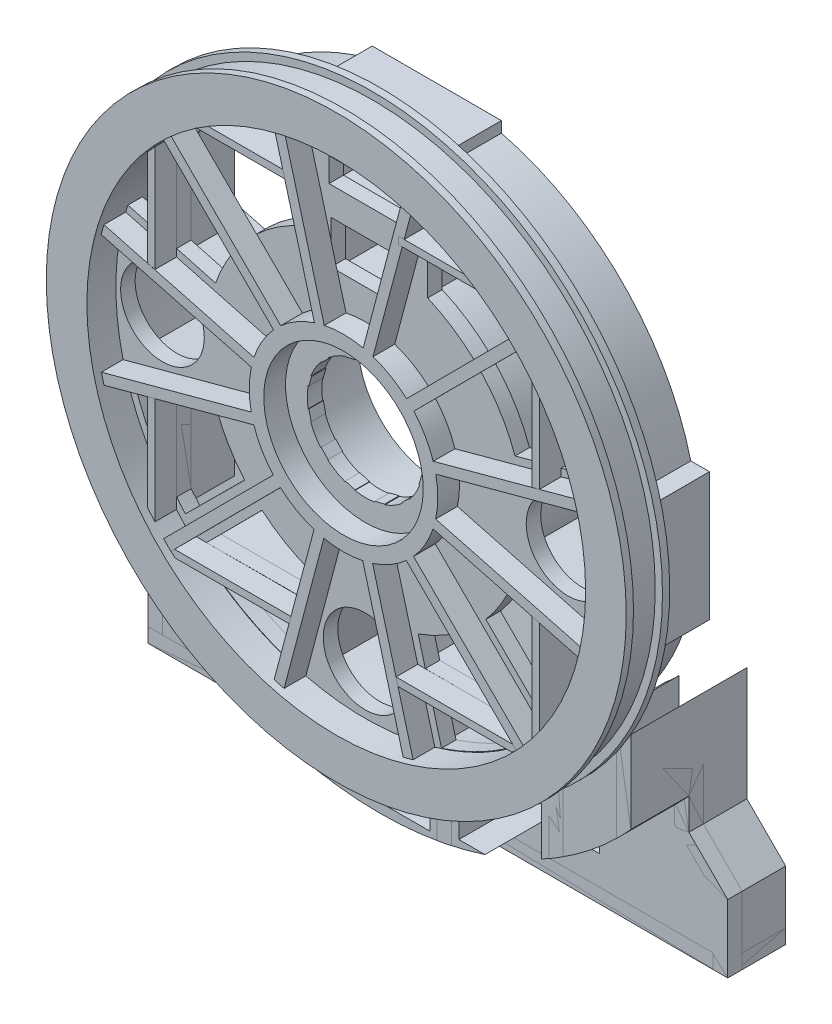
SolidWorks part; units mm, degrees
ref_plane "Front Plane" through (0, 0, 0) normal (0, 0, 1) x (1, 0, 0)
ref_plane "Top Plane" through (0, 0, 0) normal (0, 1, 0) x (1, 0, 0)
ref_plane "Right Plane" through (0, 0, 0) normal (1, 0, 0) x (0, 0, -1)
sketch "Sketch1" plane through (0, 0, 0) normal (0, 0, 1) x (1, 0, 0)
  circle A0 centre (0, 0) radius 200
extrude "Boss-Extrude1" add sketch "Sketch1" along normal blind 5
sketch "Sketch2" plane through (0, 0, 5) normal (0, 0, 1) x (1, 0, 0)
  circle A0 centre (0, 0) radius 195
extrude "Boss-Extrude2" add sketch "Sketch2" along normal blind 10
ref_plane "Plane1" through (0, 0, 15) normal (0, 0, 1) x (1, 0, 0)
mirror "Mirror2" about plane through (0, 0, 15) normal (0, 0, 1) of "Boss-Extrude2", "Boss-Extrude1"
mirror "Mirror3" about plane through (0, 0, 15) normal (0, 0, 1) of "Boss-Extrude1"
sketch "Sketch4" plane through (0, 0, 0) normal (0, 0, 1) x (1, 0, 0)
  circle A0 centre (0, 0) radius 180
  circle A1 centre (0, 0) radius 172
extrude "Boss-Extrude3" add sketch "Sketch4" against normal blind 40
sketch "Sketch5" plane through (0, 0, 0) normal (0, 0, -1) x (-1, 0, 0)
  circle A0 centre (0, 0) radius 104.5
  circle A1 centre (0, 0) radius 96.5
sketch "Sketch6" plane through (0, 0, 0) normal (0, 0, -1) x (-1, 0, 0)
  circle A0 centre (0, 0) radius 40
extrude "Cut-Extrude1" cut sketch "Sketch6" against normal through all both and the other way through all
sketch "Sketch7" plane through (0, 0, 30) normal (0, 0, 1) x (1, 0, 0)
  circle A0 centre (0, 0) radius 172
  circle A1 centre (0, 0) radius 40 construction
extrude "Cut-Extrude2" cut sketch "Sketch7" against normal blind 20
sketch "Sketch8" plane through (0, 0, 0) normal (0, 0, -1) x (-1, 0, 0)
  line L1 (-226.8867, 0) -> (327.5333, 0) construction
  line L3 (10.3528, -38.637) -> (44.5169, -166.1392) construction
sketch "Sketch11" plane through (0, 0, 0) normal (0, 0, -1) x (-1, 0, 0)
  line L0 (0, 220.657) -> (0, -234.2087) construction
  line L1 (10.3528, -38.637) -> (44.5169, -166.1392) construction
  line L3 (13.739, -37.0329) -> (48.7398, -168.4842) construction
  line L6 (41.8584, -170.3245) -> (7.0358, -38.9499) construction
  line L8 (7.0358, -38.9499) -> (13.739, -37.0329)
  line L9 (7.0358, -38.9499) -> (41.8584, -170.3245)
  line L10 (13.739, -37.0329) -> (48.7398, -168.4842)
  line L11 (41.8584, -170.3245) -> (48.7398, -168.4842)
  dimension "D1" = 15
extrude "Boss-Extrude12" add sketch "Sketch11" along normal blind 40 and the other way blind 25
pattern_circular "CirPattern7" count 12 over 360 about axis through (0, 0, 0) along (0, 0, 1) of "Boss-Extrude12"
extrude "Boss-Extrude14" add sketch "Sketch5" along normal blind 40
sketch "Sketch16" plane through (0, 0, 0) normal (0, 0, -1) x (-1, 0, 0)
  circle A0 centre (0, 0) radius 63
  circle A2 centre (0, 0) radius 55
extrude "Boss-Extrude15" add sketch "Sketch16" along normal blind 40
sketch "Sketch17" plane through (0, 0, 0) normal (0, 0, -1) x (-1, 0, 0)
  circle A0 centre (0, 0) radius 55
  circle A1 centre (0, 0) radius 40
ref_plane "Plane3" through (0, 0, -40) normal (0, 0, -1) x (-1, 0, 0)
sketch "Sketch18" plane through (0, 0, -40) normal (0, 0, -1) x (-1, 0, 0)
  circle A1 centre (0, 0) radius 55
extrude "Cut-Extrude9" cut sketch "Sketch18" against normal blind 40
sketch "Sketch20" plane through (0, 0, 0) normal (0, 0, -1) x (-1, 0, 0)
  line L0 (-76.3832, 71.3152) -> (-124.0564, 119.1386)
  line L1 (76.2988, 71.4055) -> (124.1704, 119.0198)
  line L2 (-70.7313, 65.6455) -> (-47.0532, 41.8927)
  line L3 (70.6239, 65.7611) -> (46.8523, 42.1173)
  arc A0 (76.2988, 71.4055) -> (-76.3832, 71.3152) centre (0, 0) ccw
  arc A1 (124.1704, 119.0198) -> (-124.0564, 119.1386) centre (0, 0) ccw
  arc A2 (46.8523, 42.1173) -> (-47.0532, 41.8927) centre (0, 0) ccw
  arc A3 (70.6239, 65.7611) -> (-70.7313, 65.6455) centre (0, 0) ccw
extrude "Cut-Extrude13" cut sketch "Sketch20" along normal blind 40
sketch "Sketch21" plane through (0, 0, -40) normal (0, 0, -1) x (-1, 0, 0)
  line L0 (0, 245.7288) -> (0, -237.5415) construction
  line L1 (-138.1613, 239.3024) -> (0, 0) construction
  line L2 (0, 0) -> (159.1654, 275.6826) construction
  line L3 (-33.0054, 0) -> (-33.0054, 111.1117) construction
  dimension "D1" = 30
  dimension "D2" = 60
sketch "Sketch22" plane through (0, 0, -40) normal (0, 0, -1) x (-1, 0, 0)
  line L0 (25.0054, 0) -> (25.0054, 281.7628) construction
  line L1 (-25.0054, 0) -> (-25.0054, 250.3344) construction
  line L2 (-33.0054, 0) -> (-33.0054, 111.1117) construction
  line L3 (33.0054, 0) -> (33.0054, 272.1332) construction
  line L4 (-33.0054, 0) -> (-33.0054, 250.3344) construction
  point P11 (-25.0054, 48.987)
  point P12 (-513.0578, 150.8351)
  dimension "D1" = 8
sketch "Sketch25" plane through (0, 0, -40) normal (0, 0, -1) x (-1, 0, 0)
  line L0 (-30.0323, 46.0767) -> (-30.0323, 76.987)
  line L1 (-38.0323, 39.7309) -> (-38.0323, 76.987)
  line L2 (-38.0323, 76.987) -> (38, 76.987)
  line L3 (30, 46.0977) -> (30, 76.987)
  line L4 (-38, 66.987) -> (38, 66.987)
  line L8 (38, 39.7618) -> (38, 76.987)
  line L10 (-30.0323, 176.987) -> (-30.0323, 177.4769)
  line L12 (0, 245.7288) -> (0, -237.5415) construction
  line L13 (0, 130) -> (-38.0323, 130)
  line L16 (38, 130) -> (0, 130)
  line L20 (-38.0323, 76.987) -> (-38.0323, 175.9362)
  line L21 (38, 76.987) -> (38, 175.9432)
  line L22 (30, 76.987) -> (30, 177.4824)
  line L25 (-30.0323, 76.987) -> (-30.0323, 176.987)
  line L26 (-38.0323, 122) -> (38, 122)
  arc A0 (38, 175.9432) -> (-38.0323, 175.9362) centre (0, 0) ccw
  arc A1 (38, 39.7618) -> (30, 46.0977) centre (0, 0) ccw
  arc A2 (-30.0323, 46.0767) -> (-38.0323, 39.7309) centre (0, 0) ccw
  dimension "D1" = 8
  dimension "D4" = 8
  dimension "D2" = 8
extrude "Boss-Extrude18" add sketch "Sketch25" against normal blind 40
sketch "Sketch27" plane through (0, 0, 0) normal (0, 0, -1) x (-1, 0, 0)
  line L1 (-30.0323, 122) -> (30, 122)
  line L2 (-30.0323, 122) -> (-30.0323, 76.987)
  line L3 (-30.0323, 76.987) -> (30, 76.987)
  line L4 (30, 122) -> (30, 76.987)
  line L5 (-30.0323, 122) -> (30, 76.987) construction
  line L6 (-30.0323, 76.987) -> (30, 122) construction
  line L7 (-30.0323, 66.987) -> (30, 66.987)
  line L8 (-30.0323, 66.987) -> (-30.0323, 40)
  line L9 (-30.0323, 40) -> (30, 40)
  line L10 (30, 66.987) -> (30, 40)
  line L11 (-30.0323, 66.987) -> (30, 40) construction
  line L12 (-30.0323, 40) -> (30, 66.987) construction
  point P4 (-0.0161, 99.4935)
  point P11 (-0.0161, 53.4935)
extrude "Cut-Extrude15" cut sketch "Sketch27" along normal blind 40
ref_plane "Plane4" through (0, 0, -50) normal (0, 0, -1) x (-1, 0, 0)
sketch "Sketch30" plane through (0, 0, -50) normal (0, 0, -1) x (-1, 0, 0)
  line L0 (-38.0323, 97.3334) -> (-38.0323, 167.7425) construction
  line L1 (-38.0323, 130) -> (38, 130)
  line L2 (-38.0323, 130) -> (-38.0323, 167.7425)
  line L4 (38, 130) -> (38, 167.7498)
  arc A0 (38, 167.7498) -> (-38.0323, 167.7425) centre (0, 0) ccw
  point P4 (-0.0161, 151.6509)
extrude "Cut-Extrude16" cut sketch "Sketch30" against normal blind 35
ref_plane "Plane5" through (0, 0, -40) normal (0, 0, -1) x (-1, 0, 0)
sketch "Sketch31" plane through (0, 0, -40) normal (0, 0, -1) x (-1, 0, 0)
  line L0 (-38.0323, 167.7425) -> (-38.0323, 182.0805)
  line L1 (-43.8991, 172.6431) -> (-43.8991, 166.3035)
  line L2 (38, 182.0805) -> (38, 167.7498)
  line L3 (-43.8991, 182.0805) -> (45.1952, 182.0805)
  line L8 (-43.8991, 182.0805) -> (-43.8991, 172.6431)
  line L9 (-43.8991, 172.6431) -> (45.1952, 172.6431)
  line L10 (45.1952, 182.0805) -> (45.1952, 172.6431)
  line L11 (45.1952, 172.6431) -> (45.1952, 165.956)
  arc A0 (45.1952, 165.956) -> (-43.8991, 166.3035) centre (0, 0) ccw
  point P10 (-0.0193, 178.6973)
  point P11 (0.648, 177.3618)
extrude "Boss-Extrude19" add sketch "Sketch31" against normal blind 44 contours A0 L0 L9 L1 | L8 L9 L0 L3 | L0 L9 L2 L3 | A0 L2 L9 L0 | A0 L11 L9 L2 | L10 L3 L2 L9
sketch "Sketch32" plane through (0, 0, 0) normal (0, 0, 1) x (1, 0, 0)
  line L0 (0, 0) -> (-173.1406, -99.4798)
  line L1 (0, 0) -> (0, -390) construction
  line L2 (0, 0) -> (173.1482, -99.4666)
  line L3 (173.1482, -99.4666) -> (173.1482, -389.8428)
  line L4 (-173.1406, -99.4798) -> (-173.1406, -389.8428)
  line L5 (0.0076, -199.6845) -> (0, -390)
  line L6 (173.1482, -389.8428) -> (-173.1406, -389.8428)
  line L12 (125.8692, -389.8428) -> (126.5384, -128.0157)
  line L14 (39.5868, -389.8428) -> (39.5868, -195.7212)
  line L16 (49.5868, -389.8428) -> (49.5868, -173.0351)
  line L17 (39.5868, -389.8428) -> (39.5868, -175.593)
  line L19 (-39.4279, -389.8428) -> (-39.4279, -175.6287)
  line L21 (-49.4279, -389.8428) -> (-49.4279, -173.0806)
  line L24 (-116.5381, -389.8428) -> (-116.5381, -137.1819)
  line L26 (-126.5381, -389.8428) -> (-126.5381, -128.016)
  line L28 (116.0868, -389.8428) -> (116.733, -137.0161)
  arc A0 (-173.1406, -99.4798) -> (173.1482, -99.4666) centre (0, 0) ccw
  circle A1 centre (0, 0) radius 180
  point P15 (173.1482, -99.4666)
  point P16 (-173.1406, -99.4798)
extrude "Boss-Extrude20" add sketch "Sketch32" against normal blind 80 contours A0 L28 L6 L12 | A1 L28 A0 L12 | A1 L17 A0 L16 | A0 L14 L6 L16 | A1 L21 A0 L19 | A0 L21 L6 L19 | A1 L26 A0 L24 | A0 L26 L6 L24
sketch "Sketch33" plane through (0, 0, 0) normal (0, 0, -1) x (-1, 0, 0)
  line L2 (0, 0) -> (0, -342.4917) construction
  line L3 (-173.2051, -100) -> (-173.2051, -178.3656)
  line L5 (173.2051, -100) -> (173.2051, -178.6485)
  line L6 (190, -389.8428) -> (190, -205.4434)
  line L7 (-200, -205.1605) -> (-200, -389.8428)
  line L8 (200, -205.4434) -> (200, -389.8428)
  line L9 (-173.2051, -178.3656) -> (-200, -205.1605)
  line L10 (173.2051, -178.6485) -> (200, -205.4434)
  line L13 (190, -389.8428) -> (200, -389.8428)
  line L15 (-190, -389.8428) -> (-190, -205.1605)
  line L16 (-190, -205.1605) -> (-163.2051, -178.3656)
  line L17 (-163.2051, -178.3656) -> (-163.2051, -115.6032)
  line L19 (-190, -389.8428) -> (-200, -389.8428)
  line L20 (190, -205.4434) -> (163.2051, -178.6485)
  line L21 (163.2051, -178.6485) -> (163.2051, -115.6032)
  line L22 (-190, -389.8428) -> (190, -389.8428)
  arc A0 (-173.2051, -100) -> (173.2051, -100) centre (0, 0) ccw
extrude "Boss-Extrude21" add sketch "Sketch33" along normal blind 80 separate body contours A0 L3 L9 L7 L19 L15 L16 L17 | A0 L21 L20 L6 L13 L8 L10 L5
sketch "Sketch34" plane through (0, 0, 0) normal (0, 0, -1) x (-1, 0, 0)
  line L0 (-200, -389.8428) -> (200, -389.8428)
  line L1 (200, -389.8428) -> (200, -205.4434)
  line L2 (200, -205.4434) -> (173.2051, -178.6485)
  line L3 (173.2051, -178.6485) -> (173.2051, -100)
  line L4 (-200, -389.8428) -> (-200, -205.1605)
  line L5 (-200, -205.1605) -> (-173.2051, -178.3656)
  line L6 (-173.2051, -178.3656) -> (-173.2051, -100)
  circle A0 centre (0, 0) radius 200
  circle A1 centre (0, 0) radius 200
extrude "Boss-Extrude26" add sketch "Sketch34" along normal blind 50 separate body contours A0 L6 L5 L4 L0 L1 L2 L3
ref_plane "Plane8" through (0, 0, 0) normal (-1, 0, 0) x (0, 0, 1)
sketch "Sketch38" plane through (0, 0, 0) normal (-1, 0, 0) x (0, 0, 1)
  line L0 (0, -200) -> (197.9741, -200) construction
  line L1 (30, -200) -> (30, -304.3172) construction
  line L2 (30, -200) -> (0, -200) construction
  line L3 (0, -178.3656) -> (0, -205.1605) construction
  line L4 (0, -200) -> (0, -302.6251) construction
  line L5 (0, -205.1605) -> (0, -389.8428) construction
  line L6 (0, -200) -> (-40, -166.436) construction
  line L7 (-50, -205.1605) -> (-40, -205.1605) construction
  line L8 (-80, -205.1605) -> (0, -205.1605) construction
  line L9 (-40, -205.1605) -> (-40, -166.436) construction
  line L10 (0, 0) -> (-40, -166.436)
  line L11 (-40, -166.436) -> (-40, 0) construction
  line L13 (0, 0) -> (-40, 0) construction
  point P17 (-40, -166.436)
  dimension "D2" = 166.436
  dimension "D1" = 50
sketch "Sketch39" plane through (0, 0, 10) normal (0, 0, 1) x (1, 0, 0)
  line L0 (-233.56, 0) -> (-438.1523, 0)
  line L1 (233.56, 0) -> (438.1523, 0)
  arc A0 (-233.56, 0) -> (233.56, 0) centre (0, 0) ccw
  arc A1 (-438.1523, 0) -> (438.1523, 0) centre (0, 0) ccw
extrude "Cut-Extrude17" cut sketch "Sketch39" against normal blind 40
ref_plane "Plane9" through (0, 0, 30) normal (0, 0, 1) x (1, 0, 0)
sketch "Sketch41" plane through (0, 0, 30) normal (0, 0, 1) x (1, 0, 0)
  line L0 (-306.4353, 0) -> (417.3108, 0) construction
  line L1 (0, 247.8182) -> (0, -475.0549) construction
  line L2 (0, -172) -> (470.7399, -172) construction
  line L3 (470.7399, -172) -> (-364.2612, -172) construction
  line L4 (0, -172) -> (0, -252) construction
  line L5 (-200, -389.8428) -> (200, -389.8428)
  line L6 (-200, -389.8428) -> (-200, -252)
  line L7 (200, -389.8428) -> (200, -252)
  line L8 (-200, -252) -> (200, -252)
  circle A0 centre (0, 0) radius 172 construction
  dimension "D1" = 0
extrude "Cut-Extrude18" cut sketch "Sketch41" against normal through all
sketch "Sketch42" plane through (0, 0, -40) normal (0, 0, -1) x (-1, 0, 0)
  line L0 (200, -252) -> (-200, -252)
  line L1 (200, -252) -> (200, -242)
  line L2 (-200, -252) -> (-200, -242)
  line L3 (200, -242) -> (-200, -242)
extrude "Boss-Extrude29" add sketch "Sketch42" along normal blind 40 and the other way blind 10 separate body
ref_plane "Plane10" through (0, 0, 0) normal (0, 0, -1) x (-1, 0, 0)
sketch "Sketch43" plane through (0, 0, 0) normal (0, 0, -1) x (-1, 0, 0)
  line L0 (-175.8858, 0) -> (175.8833, 0) construction
  line L4 (-187.42, -44.3248) -> (-187.42, 44.1213)
  line L12 (-187.42, -44.3248) -> (-168.5495, -44.3248)
  line L17 (-187.42, 44.1213) -> (-170.5596, 44.1213)
  line L18 (187.42, 44.357) -> (187.42, -44.0891)
  line L19 (187.42, -44.0891) -> (168.5495, -44.0891)
  line L20 (187.42, 44.357) -> (170.5596, 44.3767)
  arc A2 (170.5596, 44.3767) -> (168.5495, -44.0891) centre (18.143, 3.5843) cw
  arc A3 (-168.5495, -44.3248) -> (-170.5596, 44.1213) centre (-18.1401, 3.3395) cw
  point P0 (187.42, 0.134)
  point P1 (175.8833, 0)
  dimension "D1" = 90
  dimension "D2" = 187.42
  dimension "D3" = 187.42
  dimension "D5" = 90
extrude "Boss-Extrude31" add sketch "Sketch43" along normal blind 40
sketch "Sketch45" plane through (0, 0, -50) normal (0, 0, -1) x (-1, 0, 0)
  line L0 (205, -226.9042) -> (205, 0)
  line L1 (205, -237.3602) -> (205, -216.3758)
  line L2 (54.4279, -222) -> (111.5381, -222)
  line L3 (111.5381, -172.0007) -> (111.5381, -222)
  line L4 (54.4279, -197.6426) -> (54.4279, -222)
  line L5 (116.5381, -252) -> (116.5381, -137.1819) construction
  line L6 (49.4279, -252) -> (49.4279, -173.0806) construction
  line L7 (200, -242) -> (-200, -242) construction
  line L8 (-39.5868, -252) -> (-39.5868, -175.593) construction
  line L10 (-34.5868, -202.0613) -> (-34.5868, -227)
  line L11 (-34.5868, -227) -> (34.4279, -227)
  line L12 (34.4279, -202.0884) -> (34.4279, -227)
  line L13 (39.4279, -252) -> (39.4279, -175.6287) construction
  line L14 (-49.5868, -252) -> (-49.5868, -173.0351) construction
  line L16 (-111.5158, -172.0152) -> (-111.5158, -222)
  line L17 (-111.5158, -222) -> (-54.5868, -222)
  line L18 (-54.5868, -197.5988) -> (-54.5868, -222)
  line L19 (-116.4391, -252) -> (-116.733, -137.0161) construction
  circle A0 centre (0, 0) radius 205
  dimension "D1" = 5
  dimension "D4" = 15
  dimension "D2" = 5
  dimension "D3" = 20
  dimension "D5" = 5
  dimension "D6" = 5
  dimension "D8" = 20
  dimension "D9" = 5
  dimension "D10" = 5
extrude "Cut-Extrude19" cut sketch "Sketch45" against normal through all contours A0 L10 L11 L12 | A0 L4 L2 L3 | A0 L16 L17 L18
sketch "Sketch48" plane through (0, 0, -30) normal (0, 0, 1) x (1, 0, 0)
  line L0 (-200, -252) -> (200, -252)
  line L1 (200, -252) -> (190, -252) construction
  line L2 (200, -252) -> (200, -155.8788)
  line L4 (200, -155.8788) -> (173.9312, -155.8788)
  line L5 (-200, -155.8788) -> (-200, -252)
  line L6 (-173.9312, -155.8788) -> (-200, -155.8788)
  arc A0 (-173.9312, -155.8788) -> (173.9312, -155.8788) centre (0, 0) ccw
extrude "Cut-Extrude20" cut sketch "Sketch48" against normal blind 10
sketch "Sketch49" plane through (0, 0, 10) normal (0, 0, 1) x (1, 0, 0)
  line L0 (0, 274.6736) -> (0, -309.1586) construction
  point P0 (0, 0)
ref_plane "Plane21" through (0, 0, 10) normal (0, -1, 0) x (-1, 0, 0)
sketch "Sketch50" plane through (0, 0, 0) normal (0, 0, -1) x (-1, 0, 0)
  line L0 (354.8441, 0) -> (-354.8441, 0)
  line L1 (0, 0) -> (-280.2106, -276.0359) construction
  line L3 (-30.3739, -99.9884) -> (-48.0248, -165.1594) construction
  line L4 (-135.0788, -39.8452) -> (-130.0788, -38.5138)
  line L6 (-116.197, -126.5564) -> (-37.5696, -126.5564)
  line L7 (-116.6077, -121.5564) -> (-36.2154, -121.5564)
  line L8 (116.5332, -121.6704) -> (36.275, -121.6704)
  line L9 (116.063, -126.6704) -> (37.6063, -126.6704)
  line L12 (-130.0739, 38.637) -> (-135.0739, 39.8765)
  line L13 (-36.2154, -121.5564) -> (-37.5696, -126.5564)
  line L14 (130.0739, -38.5223) -> (135.0739, -39.8765)
  line L15 (99.9524, 30.4922) -> (165.2053, 47.8667) construction
  line L16 (116.5332, -121.6704) -> (119.0198, -124.1704)
  line L17 (165.1594, -48.0248) -> (99.9884, -30.3739) construction
  line L18 (0, 0) -> (172.4451, -297.4833) construction
  line L19 (-99.8809, 137.5279) -> (-103.2889, 137.5279)
  line L20 (99.9884, -30.3739) -> (165.1594, -48.0248) construction
  line L21 (-130.0739, 111.9589) -> (-135.0739, 106.4841)
  line L22 (130.0739, -112.0762) -> (135.0739, -106.1975)
  line L23 (-38.0323, 142.5279) -> (-95.488, 142.5279)
  line L24 (-38.0323, 137.5279) -> (-99.8809, 137.5279)
  line L25 (38, 137.5279) -> (103.2961, 137.5279)
  line L26 (38, 142.5279) -> (95.6769, 142.5279)
  line L27 (-130.0739, 38.637) -> (-130.0739, 111.9589)
  line L28 (-135.0739, 39.8765) -> (-135.0739, 106.4841)
  line L29 (135.0788, 39.8452) -> (135.0788, 106.4787)
  line L30 (130.0788, 38.6303) -> (130.0788, 111.9622)
  line L31 (-135.0788, -39.8452) -> (-135.0788, -106.1975)
  line L32 (130.0739, -38.5223) -> (130.0739, -112.0762)
  line L33 (-130.0788, -38.5138) -> (-130.0788, -112.0762)
  line L34 (135.0739, -39.8765) -> (135.0739, -106.1975)
  line L35 (95.6769, 142.5279) -> (103.2961, 137.5279)
  line L36 (-99.9884, 30.3739) -> (-165.1594, 48.0248) construction
  line L37 (-95.488, 142.5279) -> (-103.2889, 137.5279)
  line L38 (-38.0323, 142.5279) -> (-38.0323, 137.5279)
  line L39 (38, 142.5279) -> (38, 137.5279)
  line L40 (71.4055, -76.2988) -> (119.0198, -124.1704) construction
  line L41 (130.0788, 111.9622) -> (135.0788, 106.4787)
  line L42 (36.275, -121.6704) -> (37.6063, -126.6704)
  line L43 (130.0788, 38.6303) -> (135.0788, 39.8452)
  line L44 (30.4922, -99.9524) -> (47.8667, -165.2053) construction
  line L45 (-48.0248, -165.1594) -> (-30.3739, -99.9884) construction
  line L46 (119.0198, -124.1704) -> (116.063, -126.6704)
  line L47 (-116.6077, -121.5564) -> (-119.1386, -124.0564)
  line L48 (-119.1386, -124.0564) -> (-116.197, -126.5564)
  line L49 (-99.9524, -30.4922) -> (-165.2053, -47.8667) construction
  line L52 (-135.0788, -106.1975) -> (-130.0788, -112.0762)
  arc A6 (165.2053, 47.8667) -> (38, 167.7498) centre (0, 0) ccw construction
  point P7 (0, 0)
  dimension "D1" = 44.57
  dimension "D6" = 59.9
extrude "Boss-Extrude35" add sketch "Sketch50" along normal blind 30 and the other way blind 25 separate body contours L31 L52 L33 L4 | L27 L21 L28 L12 | L23 L37 L19 L24 L38 | L26 L35 L25 L39 | L30 L41 L29 L43 | L32 L22 L34 L14 | L8 L42 L9 L46 L16 | L6 L13 L7 L47 L48
sketch "Sketch51" plane through (0, 0, 0) normal (0, 0, -1) x (-1, 0, 0)
  line L1 (-94.7674, 137.5069) -> (-43.0323, 137.5279)
  line L2 (-38.0323, 137.5279) -> (-103.2889, 137.5279) construction
  line L4 (42.7713, -126.6358) -> (116.063, -126.6704)
  line L5 (-130.0739, 104.7368) -> (-130.0739, 43.7024)
  line L6 (41.4023, -121.4944) -> (36.5376, -103.2243)
  line L8 (-163.8523, 52.8509) -> (-98.6813, 35.2001)
  line L9 (-130.0739, 43.7024) -> (-103.2588, 36.4398)
  line L11 (-130.0739, 38.637) -> (-130.0739, 111.9589) construction
  line L13 (-43.0323, 142.5279) -> (-95.488, 142.5279)
  line L16 (-38.0323, 142.5279) -> (-95.488, 142.5279) construction
  line L17 (-43.0323, 100.69) -> (-43.0323, 137.5279)
  line L18 (-95.488, 142.5279) -> (-103.2889, 137.5279) construction
  line L19 (-43.0323, 142.5279) -> (-43.0323, 166.4828)
  line L20 (-127.6964, -115.4748) -> (-79.8248, -67.8605)
  line L21 (-124.0301, -111.8282) -> (-83.1873, -71.2049)
  line L22 (-130.0739, -43.6867) -> (-130.0788, -104.7306)
  line L23 (-163.9188, -52.6984) -> (-98.6659, -35.3239)
  line L24 (-158.905, -51.3634) -> (-135.0788, -45.0194)
  line L25 (-130.0788, -38.5138) -> (-130.0788, -112.0762) construction
  line L26 (-135.0788, -45.0194) -> (-135.0788, -98.1973)
  line L27 (-135.0788, -39.8452) -> (-135.0788, -106.1975) construction
  line L28 (-130.0739, -43.6867) -> (-103.2243, -36.5376)
  line L29 (0, 0) -> (0, 235.0642) construction
  line L30 (130.0739, 43.7024) -> (103.2588, 36.4398)
  line L31 (43.0323, 142.5279) -> (43.0323, 166.4828)
  line L32 (43.0323, 142.5279) -> (95.488, 142.5279)
  line L33 (130.0739, 104.7368) -> (130.0739, 43.7024)
  line L34 (94.7674, 137.5069) -> (43.0323, 137.5279)
  line L35 (43.0323, 100.69) -> (43.0323, 137.5279)
  line L36 (135.0788, -45.0194) -> (135.0788, -98.1973)
  line L37 (158.905, -51.3634) -> (135.0788, -45.0194)
  line L38 (130.0739, -43.6867) -> (103.2243, -36.5376)
  line L39 (130.0739, -43.6867) -> (130.0788, -104.7306)
  line L40 (124.0301, -111.8282) -> (83.1873, -71.2049)
  line L41 (-41.4023, -121.4944) -> (-109.4812, -121.6704)
  line L42 (-41.4023, -121.4944) -> (-36.5376, -103.2243)
  line L43 (-109.4812, -121.6704) -> (-71.2049, -83.1873)
  line L44 (115.4748, -127.6964) -> (67.8605, -79.8248)
  line L45 (109.4812, -121.6704) -> (71.2049, -83.1873)
  line L46 (41.4023, -121.4944) -> (109.4812, -121.6704)
  line L47 (52.6984, -163.9188) -> (35.3239, -98.6659)
  line L48 (52.5867, -163.4991) -> (42.7713, -126.6358)
  line L49 (116.5332, -121.6704) -> (36.275, -121.6704) construction
  line L50 (-42.7713, -126.6358) -> (-116.063, -126.6704)
  line L51 (-52.5867, -163.4991) -> (-42.7713, -126.6358)
  line L52 (-30.0323, 169.3578) -> (-30.0323, 130) construction
  line L57 (23.6396, 85.8453) -> (-23.6396, 85.8453)
  line L58 (23.6396, 85.8453) -> (23.6396, 115.5347)
  line L59 (23.6396, 115.5347) -> (-23.6396, 115.5347)
  line L60 (-23.6396, 85.8453) -> (-23.6396, 115.5347)
  line L61 (23.6396, 85.8453) -> (-23.6396, 115.5347) construction
  line L62 (23.6396, 115.5347) -> (-23.6396, 85.8453) construction
  line L67 (-30.0323, 156.7307) -> (30, 156.7307)
  line L69 (-30.0323, 151.7307) -> (30, 151.7307)
  line L71 (30, 130) -> (30, 169.3635) construction
  line L72 (30, 130) -> (-30.0323, 130) construction
  line L73 (-25.0323, 151.7307) -> (25, 151.7307)
  line L74 (-25.0323, 151.7307) -> (-25.0323, 135)
  line L75 (-25.0323, 135) -> (25, 135)
  line L76 (25, 151.7307) -> (25, 135)
  line L77 (-135.0739, 45.0566) -> (-163.6928, 52.8078)
  line L78 (-25.0323, 156.7307) -> (25, 156.7307)
  line L79 (-25.0323, 156.7307) -> (-25.0323, 167.599)
  line L80 (-25.0323, 167.599) -> (25, 167.599)
  line L81 (25, 156.7307) -> (25, 167.599)
  line L82 (-135.0739, 45.0566) -> (-135.0739, 106.485)
  line L83 (-135.0739, 39.8765) -> (-135.0739, 106.4841) construction
  line L84 (135.0739, 45.0566) -> (135.0739, 106.485)
  line L85 (135.0739, 45.0566) -> (163.6928, 52.8078)
  arc A0 (52.5867, -163.4991) -> (116.063, -126.6704) centre (-3.5112, 6.3055) ccw
  arc A1 (-95.488, 142.5279) -> (-43.0323, 166.4828) centre (4.6666, -7.377) cw
  arc A2 (-130.0788, -104.7306) -> (-124.0301, -111.8282) centre (0, 0) ccw
  arc A3 (-104.7348, -31.9512) -> (-79.9494, -74.822) centre (0, 0) ccw
  arc A4 (-103.2243, -36.5376) -> (-83.1873, -71.2049) centre (0, 0) ccw
  arc A5 (-36.9267, 162.8663) -> (-160.3582, 46.6287) centre (0, 0) ccw
  arc A6 (-160.4028, -46.4753) -> (-120.5608, -115.5599) centre (0, 0) ccw
  arc A8 (-94.7674, 137.5069) -> (-130.0739, 104.7368) centre (0, 0) ccw
  arc A9 (-158.905, -51.3634) -> (-135.0788, -98.1973) centre (0, 0) ccw
  arc A10 (95.488, 142.5279) -> (43.0323, 166.4828) centre (-4.6666, -7.377) ccw
  arc A11 (94.7674, 137.5069) -> (130.0739, 104.7368) centre (0, 0) cw
  arc A12 (43.0323, 100.69) -> (103.2588, 36.4398) centre (0, 0) cw
  arc A13 (158.905, -51.3634) -> (135.0788, -98.1973) centre (0, 0) cw
  arc A14 (130.0788, -104.7306) -> (124.0301, -111.8282) centre (0, 0) cw
  arc A15 (103.2243, -36.5376) -> (83.1873, -71.2049) centre (0, 0) cw
  arc A16 (-39.852, 101.9905) -> (-104.7725, 31.8272) centre (0, 0) ccw
  arc A17 (-43.0323, 100.69) -> (-103.2588, 36.4398) centre (0, 0) ccw
  arc A18 (-36.5376, -103.2243) -> (-71.2049, -83.1873) centre (0, 0) cw
  arc A19 (-52.5867, -163.4991) -> (-116.063, -126.6704) centre (3.5112, 6.3055) cw
  arc A20 (31.9512, -104.7348) -> (74.822, -79.9494) centre (0, 0) ccw
  arc A21 (36.5376, -103.2243) -> (71.2049, -83.1873) centre (0, 0) ccw
  circle A22 centre (139.8725, 0) radius 28.8717
  circle A23 centre (0, -137.8644) radius 28.9807
  circle A24 centre (-139.8725, 0) radius 28.8717
  arc A25 (165.2053, 47.8667) -> (-165.1594, 48.0248) centre (0, 0) ccw construction
  arc A26 (-163.6928, 52.8078) -> (-135.0739, 106.485) centre (0, 0) cw
  arc A27 (163.6928, 52.8078) -> (135.0739, 106.485) centre (0, 0) ccw
  point P42 (-43.0323, 166.4828)
  point P100 (0, 100.69)
  dimension "D10" = 5
  dimension "D8" = 5
  dimension "D11" = 5
  dimension "D12" = 5
  dimension "D13" = 5
  dimension "D14" = 5
  dimension "D1" = 5
  dimension "D2" = 5
  dimension "D3" = 5
  dimension "D4" = 5
  dimension "D5" = 5
  dimension "D6" = 5
  dimension "D7" = 5
  dimension "D9" = 5
extrude "Cut-Extrude22" cut sketch "Sketch51" against normal blind 10.1 contours A17 L17 L1 A8 L5 L9 | L35 A12 L30 L33 A11 L34 | L60 L57 L58 L59 | L76 L69 L74 L75 | L67 L81 L80 L79 | A22 | A24 | A23 | A19 L51 L50 | L42 A18 L43 L41 | A4 L28 L22 A2 L21 | L24 A9 L26 | L48 A0 L4 | A21 L6 L46 L45 | L38 A15 L40 A14 L39 | A13 L37 L36 | L13 A1 L19 | L31 A10 L32 | L77 A26 L82 | L84 A27 L85
sketch "Sketch54" plane through (0, 0, 10) normal (0, 0, 1) x (1, 0, 0)
  circle A0 centre (0, 0) radius 55
  circle A1 centre (0, 0) radius 65
extrude "Boss-Extrude36" add sketch "Sketch54" along normal blind 15
sketch "Sketch55" plane through (0, 0, 25) normal (0, 0, 1) x (1, 0, 0)
  circle A0 centre (0, 0) radius 55
extrude "Cut-Extrude23" cut sketch "Sketch55" against normal blind 15
